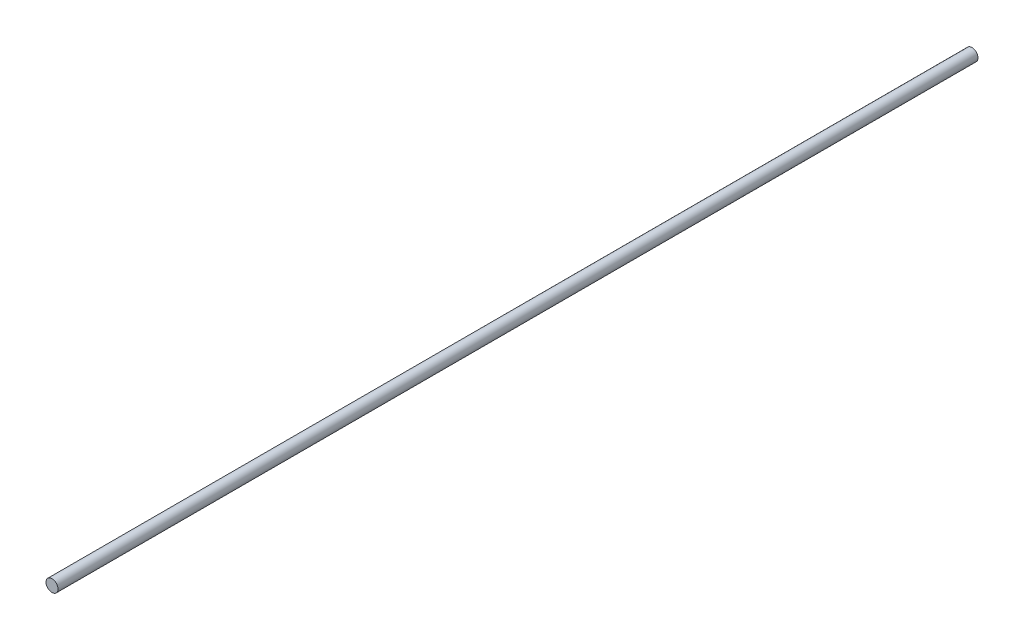
SolidWorks part; units mm, degrees
ref_plane "前视基准面" through (0, 0, 0) normal (0, 0, 1) x (1, 0, 0)
ref_plane "上视基准面" through (0, 0, 0) normal (0, 1, 0) x (1, 0, 0)
ref_plane "右视基准面" through (0, 0, 0) normal (1, 0, 0) x (0, 0, -1)
other "Configuration Table"
sketch "草图1" plane through (0, 0, 0) normal (0, 0, 1) x (1, 0, 0)
  circle A0 centre (-2.4976, 4.4922) radius 13.05
  dimension "D1" = 26.1
extrude "凸台-拉伸1" add sketch "草图1" along normal blind 2000
